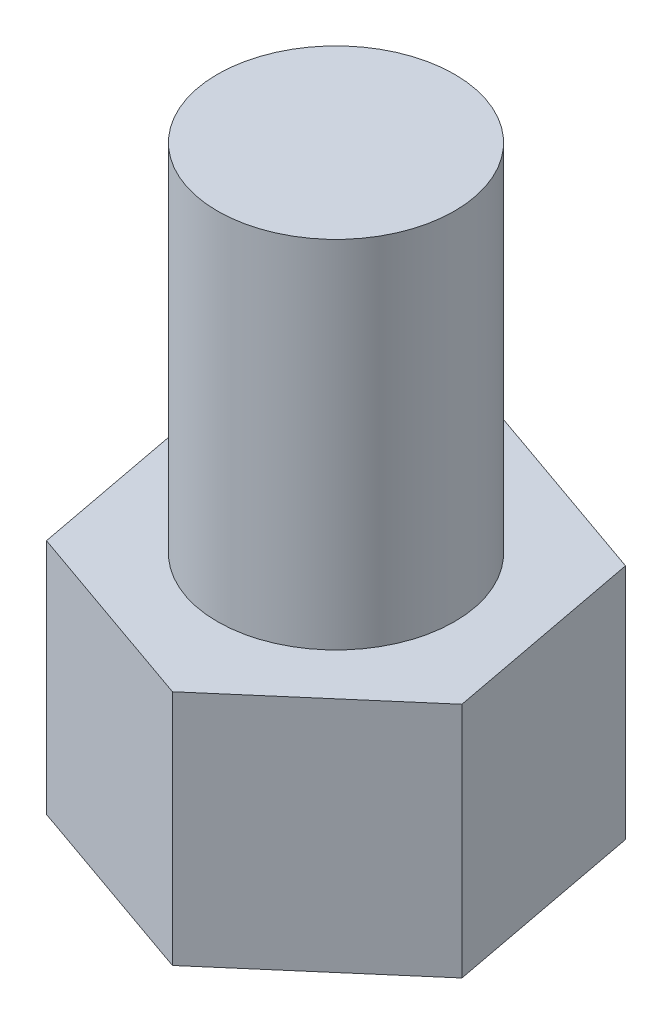
SolidWorks part; units mm, degrees
ref_plane "前视基准面" through (0, 0, 0) normal (0, 0, 1) x (1, 0, 0)
ref_plane "上视基准面" through (0, 0, 0) normal (0, 1, 0) x (1, 0, 0)
ref_plane "右视基准面" through (0, 0, 0) normal (1, 0, 0) x (0, 0, -1)
sketch "草图1" plane through (0, 0, 0) normal (0, 1, 0) x (1, 0, 0)
  line L1 (1.6348, -0.5722) -> (1.3129, 1.1297)
  line L2 (1.3129, 1.1297) -> (-0.3219, 1.7019)
  line L3 (-0.3219, 1.7019) -> (-1.6348, 0.5722)
  line L4 (-1.6348, 0.5722) -> (-1.3129, -1.1297)
  line L5 (-1.3129, -1.1297) -> (0.3219, -1.7019)
  line L6 (0.3219, -1.7019) -> (1.6348, -0.5722)
  circle A0 centre (0, 0) radius 1.5 construction
  dimension "D1" = 3
extrude "凸台-拉伸1" add sketch "草图1" along normal blind 2
sketch "草图2" plane through (0, 2, 0) normal (0, 1, 0) x (1, 0, 0)
  circle A0 centre (0, 0) radius 1
  dimension "D1" = 2
extrude "凸台-拉伸2" add sketch "草图2" along normal blind 3
